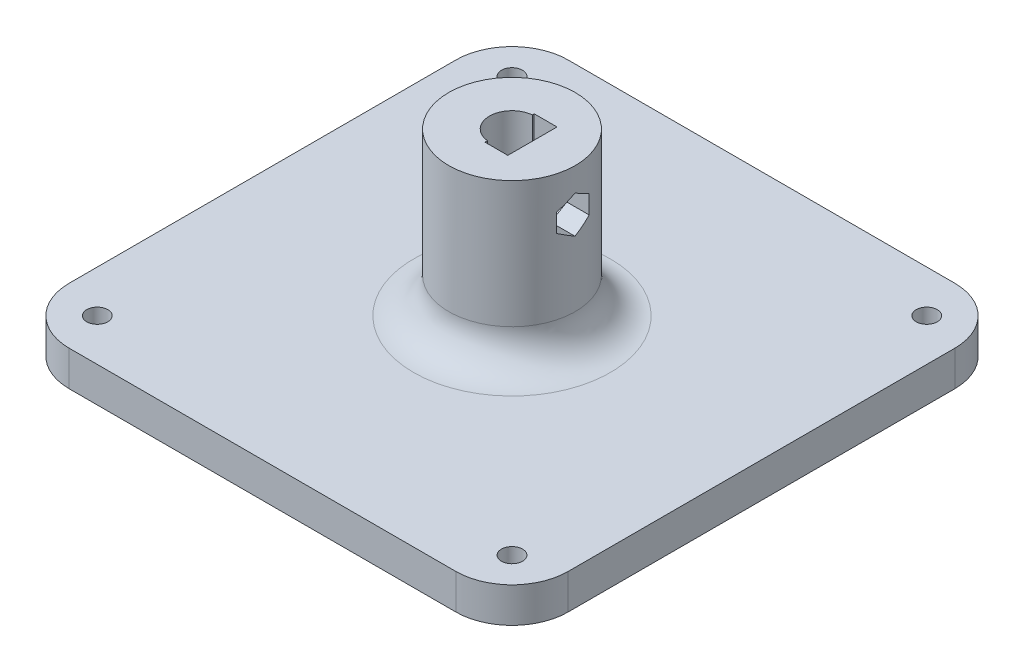
SolidWorks part; units mm, degrees
ref_plane "Front Plane" through (0, 0, 0) normal (0, 0, 1) x (1, 0, 0)
ref_plane "Top Plane" through (0, 0, 0) normal (0, 1, 0) x (1, 0, 0)
ref_plane "Right Plane" through (0, 0, 0) normal (1, 0, 0) x (0, 0, -1)
sketch "Sketch1" plane through (0, 0, 0) normal (0, 1, 0) x (1, 0, 0)
  line L1 (0, 0) -> (71, 0)
  line L2 (0, 0) -> (0, 71)
  line L3 (0, 71) -> (71, 71)
  line L4 (71, 0) -> (71, 71)
  dimension "D1" = 71
  dimension "D2" = 71
extrude "Boss-Extrude1" add sketch "Sketch1" along normal blind 5
sketch "Sketch2" plane through (0, 5, 0) normal (0, 1, 0) x (1, 0, 0)
  circle A0 centre (35.5, 35.5) radius 9
  point P0 (35.5, 35.5)
  dimension "D1" = 18
extrude "Boss-Extrude2" add sketch "Sketch2" along normal blind 23
fillet "Fillet1" radius 5 1 edges at (35.5, 5, -44.5)
sketch "Sketch3" plane through (0, 28, 0) normal (0, 1, 0) x (1, 0, 0)
  line L1 (37.7, 38.5) -> (40.8932, 38.5)
  line L2 (37.7, 38.5) -> (37.7, 32.5)
  line L3 (37.7, 32.5) -> (40.8932, 32.5)
  line L4 (40.8932, 38.5) -> (40.8932, 32.5)
  circle A0 centre (35.5, 35.5) radius 3.2
  point P0 (35.5, 35.5)
  dimension "D1" = 6.4
  dimension "D2" = 2.2
extrude "Cut-Extrude1" cut sketch "Sketch3" against normal blind 46 contours L2 A0
fillet "Fillet2" radius 8 4 edges at (0, 2.5, 0) (71, 2.5, 0) (71, 2.5, -71) (0, 2.5, -71)
sketch "Sketch4" plane through (0, 5, 0) normal (0, 1, 0) x (1, 0, 0)
  line L0 (63, 71) -> (8, 71) construction
  line L1 (71, 8) -> (71, 63) construction
  line L2 (8, 0) -> (63, 0) construction
  line L3 (0, 63) -> (0, 8) construction
  circle A0 centre (65, 65) radius 1.5
  circle A1 centre (65, 6) radius 1.5
  circle A2 centre (6, 6) radius 1.5
  circle A3 centre (6, 65) radius 1.5
  dimension "D1" = 3
  dimension "D6" = 3
  dimension "D9" = 3
  dimension "D12" = 3
  dimension "D2" = 6
  dimension "D3" = 6
  dimension "D4" = 6
  dimension "D5" = 6
  dimension "D7" = 6
  dimension "D8" = 6
  dimension "D10" = 6
  dimension "D11" = 6
extrude "Cut-Extrude2" cut sketch "Sketch4" against normal through all
sketch "Sketch5" plane through (0, 0, 0) normal (0, -1, 0) x (-1, 0, 0)
  line L1 (-43.8138, 35.5) -> (-39.6569, 28.3)
  line L2 (-39.6569, 28.3) -> (-31.3431, 28.3)
  line L3 (-31.3431, 28.3) -> (-27.1862, 35.5)
  line L4 (-27.1862, 35.5) -> (-31.3431, 42.7)
  line L5 (-31.3431, 42.7) -> (-39.6569, 42.7)
  line L6 (-39.6569, 42.7) -> (-43.8138, 35.5)
  circle A0 centre (-35.5, 35.5) radius 7.2 construction
  point P0 (-35.5, 35.5)
  dimension "D1" = 14.4
extrude "Cut-Extrude3" cut sketch "Sketch5" against normal blind 10
sketch "Sketch6" plane through (37.7, 0, 0) normal (-1, 0, 0) x (0, 0, 1)
  line L0 (-33.1762, 10) -> (-33.1762, 28) construction
  line L1 (-35.4562, 26.0415) -> (-38.9562, 24.0207)
  line L2 (-38.9562, 24.0207) -> (-38.9562, 19.9793)
  line L3 (-38.9562, 19.9793) -> (-35.4562, 17.9585)
  line L4 (-35.4562, 17.9585) -> (-31.9562, 19.9793)
  line L5 (-31.9562, 19.9793) -> (-31.9562, 24.0207)
  line L6 (-31.9562, 24.0207) -> (-35.4562, 26.0415)
  line L7 (-37.8238, 28) -> (-33.1762, 28) construction
  circle A0 centre (-35.4562, 22) radius 3.5 construction
  dimension "D1" = 7
  dimension "D2" = 2.28
  dimension "D3" = 6
extrude "Cut-Extrude4" cut sketch "Sketch6" against normal blind 3.35 and the other way blind 2.5
fillet "Fillet3" radius 0.5 6 edges at (41.05, 18.9689, -33.7062) (41.05, 22, -31.9562) (41.05, 25.0311, -33.7062) (41.05, 25.0311, -37.2062) (41.05, 22, -38.9562) (41.05, 18.9689, -37.2062)
sketch "Sketch10" plane through (41.05, 0, 0) normal (-1, 0, 0) x (0, 0, 1)
  line L1 (-35.4562, 24.6293) -> (-37.7562, 23.3014)
  line L2 (-37.7562, 23.3014) -> (-37.7562, 20.6456)
  line L3 (-37.7562, 20.6456) -> (-35.4562, 19.3177)
  line L4 (-35.4562, 19.3177) -> (-33.1562, 20.6456)
  line L5 (-33.1562, 20.6456) -> (-33.1562, 23.3014)
  line L6 (-33.1562, 23.3014) -> (-35.4562, 24.6293)
  circle A0 centre (-35.4562, 21.9735) radius 2.3 construction
  dimension "D1" = 4.6
extrude "Cut-Extrude9" cut sketch "Sketch10" against normal through all
sketch "Sketch11" plane through (0, 28, 0) normal (0, 1, 0) x (1, 0, 0)
  line L0 (35.2, 38.9562) -> (40.55, 38.9562) construction
  line L1 (35.2, 31.9562) -> (38.4482, 31.9562)
  line L2 (35.2, 31.9562) -> (35.2, 38.9562)
  line L3 (35.2, 38.9562) -> (38.4482, 38.9562)
  line L4 (38.4482, 31.9562) -> (38.4482, 38.9562)
extrude "Cut-Extrude10" cut sketch "Sketch11" against normal blind 5
